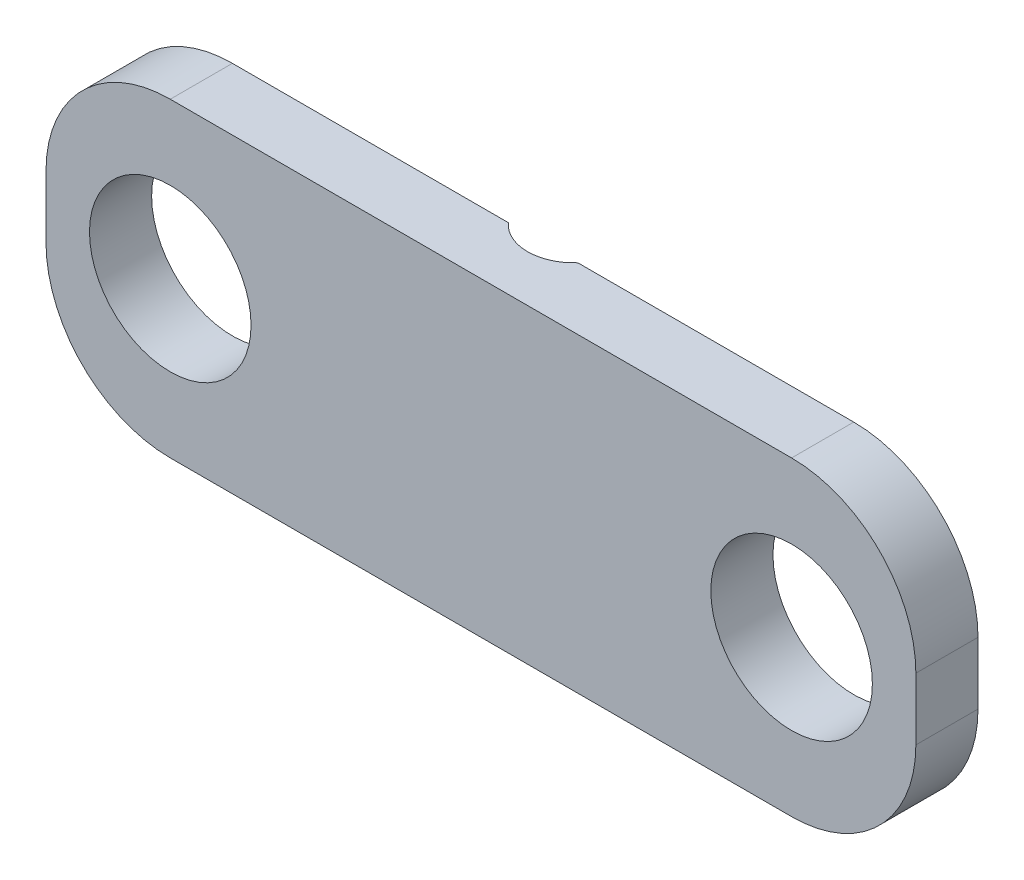
SolidWorks part; units mm, degrees
ref_plane "Front Plane" through (0, 0, 0) normal (0, 0, 1) x (1, 0, 0)
ref_plane "Top Plane" through (0, 0, 0) normal (0, 1, 0) x (1, 0, 0)
ref_plane "Right Plane" through (0, 0, 0) normal (1, 0, 0) x (0, 0, -1)
sketch "Sketch2" plane through (0, 0, 0) normal (0, 0, 1) x (1, 0, 0)
  line L0 (-14.0871, 0) -> (10.1566, 0) construction
  line L1 (-5, 2.5) -> (5, 2.5)
  line L2 (-7, 0.5) -> (-7, -0.5)
  line L3 (-5, -2.5) -> (5, -2.5)
  line L4 (7, 0.5) -> (7, -0.5)
  line L5 (-7, 2.5) -> (7, -2.5) construction
  line L6 (-7, -2.5) -> (7, 2.5) construction
  line L7 (0, -2.5) -> (0, 2.5) construction
  arc A0 (5, -2.5) -> (7, -0.5) centre (5, -0.5) ccw
  arc A1 (-7, -0.5) -> (-5, -2.5) centre (-5, -0.5) ccw
  arc A2 (-5, 2.5) -> (-7, 0.5) centre (-5, 0.5) ccw
  arc A3 (5, 2.5) -> (7, 0.5) centre (5, 0.5) cw
  point P0 (0, 0)
  point P8 (5, 0)
  point P11 (-5, 0)
  dimension "D4" = 2
  dimension "D1" = 14
  dimension "D2" = 5
  dimension "D3" = 2
extrude "Boss-Extrude1" add sketch "Sketch2" along normal blind 1
hole_wizard "M2 Clearance Hole1" positions "Sketch13" profile "Sketch12" hole size "M2" standard "ANSI Metric" end condition up to next
sketch "Sketch13" plane through (0, 0, 0) normal (0, 0, -1) x (-1, 0, 0)
  point P0 (-5, 0)
  point P3 (5, 0)
sketch "Sketch12" plane through (5, 0, 0) normal (1, 0, 0) x (0, 1, 0)
  line L0 (0, 0) -> (0, 1)
  line L1 (0, 1) -> (1.3, 1)
  line L2 (1.3, 1) -> (1.3, 0)
  line L5 (1.3, 0) -> (0, 0)
  line L11 (0, -6.35) -> (0, 107.95) construction
  dimension "Thru Hole Dia." = 2.6
  dimension "Thru Hole Depth" = 1
sketch "Sketch15" plane through (0, -2.5, 0) normal (0, -1, 0) x (1, 0, 0)
  line L0 (0, -2.0861) -> (0, 2.0861) construction
  line L1 (-5, 0) -> (5, 0) construction
  circle A0 centre (0, -0.5) radius 0.75
  point P2 (0, 0)
  dimension "D1" = 1.5
  dimension "D2" = 0.5
extrude "Cut-Extrude1" cut sketch "Sketch15" against normal up to next
equation "\"D2@Sketch15\"=1.50mm/3"
